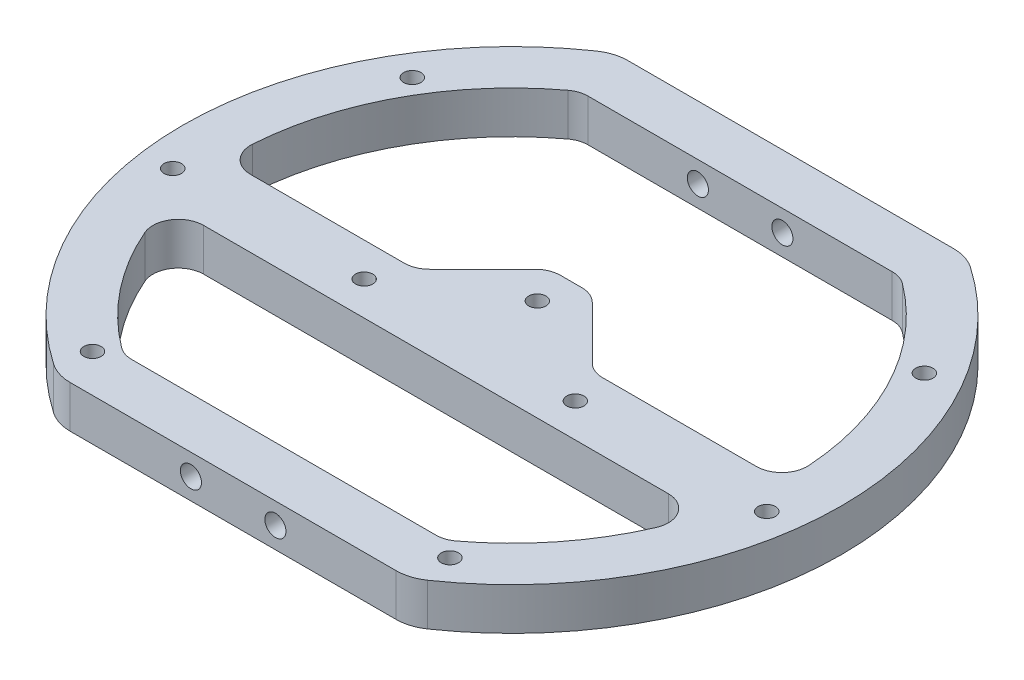
SolidWorks part; units mm, degrees
ref_plane "Front Plane" through (0, 0, 0) normal (0, 0, 1) x (1, 0, 0)
ref_plane "Top Plane" through (0, 0, 0) normal (0, 1, 0) x (1, 0, 0)
ref_plane "Right Plane" through (0, 0, 0) normal (1, 0, 0) x (0, 0, -1)
sketch "Sketch1" plane through (0, 0, 0) normal (0, 1, 0) x (1, 0, 0)
  line L0 (-20.7846, 33) -> (20.7846, 33)
  line L1 (-20.7846, -33) -> (20.7846, -33)
  line L2 (0, 33) -> (0, -33) construction
  arc A0 (-20.7846, 33) -> (-20.7846, -33) centre (0, 0) ccw
  arc A1 (20.7846, -33) -> (20.7846, 33) centre (0, 0) ccw
  point P9 (0, 0)
  dimension "D1" = 78
  dimension "D2" = 66
extrude "Boss-Extrude1" add sketch "Sketch1" along normal blind 5
fillet "Fillet1" radius 5 4 edges at (-20.7846, 2.5, -33) (20.7846, 2.5, -33) (-20.7846, 2.5, 33) (20.7846, 2.5, 33)
hole_wizard "M3x0.5 Tapped Hole1" positions "Sketch2" profile "Sketch3" tap size "M3x0.5" standard "ANSI Metric"
sketch "Sketch2" plane through (0, 0, 33) normal (0, 0, 1) x (1, 0, 0)
  line L0 (0, 0) -> (0, 5) construction
  line L1 (-19.2873, 0) -> (19.2873, 0) construction
  line L2 (-19.2873, 5) -> (19.2873, 5) construction
  line L5 (-5, 2.5) -> (5, 2.5) construction
  point P0 (-5, 2.5)
  point P2 (5, 2.5)
  point P18 (0, 2.5)
  dimension "D1" = 10
sketch "Sketch3" plane through (-5, 2.5, 33) normal (1, 0, 0) x (0, -1, 0)
  line L0 (0, 0) -> (0, 8.2511)
  line L1 (0, 8.2511) -> (1.25, 7.5)
  line L2 (1.25, 7.5) -> (1.25, 0)
  line L5 (1.25, 0) -> (0, 0)
  line L10 (0, 8.2511) -> (-1.25, 7.5) construction
  line L11 (0, -6.35) -> (0, 107.95) construction
  dimension "Tap Drill Dia." = 2.5
  dimension "Tap Drill Depth" = 7.5
  dimension "Drill Angle" = 118
cosmetic thread "Hole Thread1" parameters "D1"=6, "D2"=3
cosmetic thread "Hole Thread2" parameters "D1"=6, "D2"=3
mirror "Mirror1" about plane through (0, 0, 0) normal (0, 0, 1) of "M3x0.5 Tapped Hole1"
cosmetic thread "Hole Thread3" parameters "D1"=6, "D2"=3
cosmetic thread "Hole Thread4" parameters "D1"=6, "D2"=3
hole_wizard "M2.5x0.45 Tapped Hole2" positions "Sketch4" profile "Sketch5" tap size "M2.5x0.45" standard "ANSI Metric" end condition through all
sketch "Sketch4" plane through (0, 0, 0) normal (0, -1, 0) x (-1, 0, 0)
  line L0 (12.5, -5) -> (-12.5, -5) construction
  point P0 (12.5, -5)
  point P2 (-12.5, -5)
  point P8 (0, -5)
  point P10 (0, 3)
  dimension "D1" = 25
  dimension "D2" = 5
  dimension "D3" = 8
sketch "Sketch5" plane through (-12.5, 0, 5) normal (1, 0, 0) x (0, 0, -1)
  line L0 (0, 0) -> (0, 5)
  line L1 (0, 5) -> (1.025, 5)
  line L2 (1.025, 5) -> (1.025, 0)
  line L5 (1.025, 0) -> (0, 0)
  line L11 (0, -6.35) -> (0, 107.95) construction
  dimension "Thru Tap Drill Dia." = 2.05
  dimension "Thru Tap Drill Depth" = 5
cosmetic thread "Hole Thread5" parameters "D2"=2.5
cosmetic thread "Hole Thread6" parameters "D2"=2.5
cosmetic thread "Hole Thread7" parameters "D2"=2.5
sketch "Sketch6" plane through (0, 0, 0) normal (0, -1, 0) x (1, 0, 0)
  line L2 (-31.749, 9) -> (31.749, 9)
  line L3 (32.9848, 1) -> (10.5, 1)
  line L4 (-18.9737, -27) -> (18.9737, -27)
  line L5 (18.9737, 27) -> (-18.9737, 27)
  line L6 (-18.9737, -27) -> (18.9737, -27)
  line L7 (18.9737, 27) -> (-18.9737, 27)
  line L8 (-32.619, 5) -> (32.619, 5) construction
  line L10 (-10.5, 1) -> (-2.5, -7)
  line L11 (2.5, -7) -> (10.5, 1)
  line L12 (-10.5, 1) -> (-32.9848, 1)
  line L13 (-2.5, -7) -> (2.5, -7)
  line L14 (0, -7) -> (0, 0) construction
  arc A0 (-32.9848, 1) -> (-18.9737, -27) centre (0, 0) ccw
  arc A1 (31.749, 9) -> (18.9737, 27) centre (0, 0) ccw
  arc A12 (-18.9737, 27) -> (-18.9737, -27) centre (0, 0) ccw
  arc A13 (18.9737, -27) -> (18.9737, 27) centre (0, 0) ccw
  arc A14 (-18.9737, 27) -> (-31.749, 9) centre (0, 0) ccw
  arc A15 (18.9737, -27) -> (32.9848, 1) centre (0, 0) ccw
  point P6 (-12.5, 5)
  dimension "D2" = 8
  dimension "D3" = 8
  dimension "D4" = 5
  dimension "D1" = 6
extrude "Cut-Extrude1" cut sketch "Sketch6" against normal up to surface (5 mm away) up to face at (-12.5, 5, 3.975)
fillet "Fillet2" radius 3 12 edges at (18.9737, 2.5, -27) (-18.9737, 2.5, -27) (32.9848, 2.5, 1) (-31.749, 2.5, 9) (18.9737, 2.5, 27) (31.749, 2.5, 9) (-18.9737, 2.5, 27) (-32.9848, 2.5, 1) (-10.5, 2.5, 1) (10.5, 2.5, 1) (-2.5, 2.5, -7) (2.5, 2.5, -7)
hole_wizard "M2.5x0.45 Tapped Hole1" positions "Sketch7" profile "Sketch8" tap size "M2.5x0.45" standard "ANSI Metric" end condition through all
sketch "Sketch7" plane through (0, 0, 0) normal (0, -1, 0) x (-1, 0, 0)
  point P0 (-21.15, -28.5)
  point P3 (21.15, -28.5)
  point P6 (30.3, 18.5)
  point P9 (-30.3, 18.5)
  point P12 (-35.15, -5)
  point P30 (35.15, -5)
sketch "Sketch8" plane through (21.15, 0, 28.5) normal (1, 0, 0) x (0, 0, -1)
  line L0 (0, 0) -> (0, 5)
  line L1 (0, 5) -> (1.025, 5)
  line L2 (1.025, 5) -> (1.025, 0)
  line L5 (1.025, 0) -> (0, 0)
  line L11 (0, -6.35) -> (0, 107.95) construction
  dimension "Thru Tap Drill Dia." = 2.05
  dimension "Thru Tap Drill Depth" = 5
cosmetic thread "Hole Thread8" parameters "D2"=2.5
cosmetic thread "Hole Thread9" parameters "D2"=2.5
cosmetic thread "Hole Thread10" parameters "D2"=2.5
cosmetic thread "Hole Thread11" parameters "D2"=2.5
cosmetic thread "Hole Thread12" parameters "D2"=2.5
cosmetic thread "Hole Thread13" parameters "D2"=2.5
